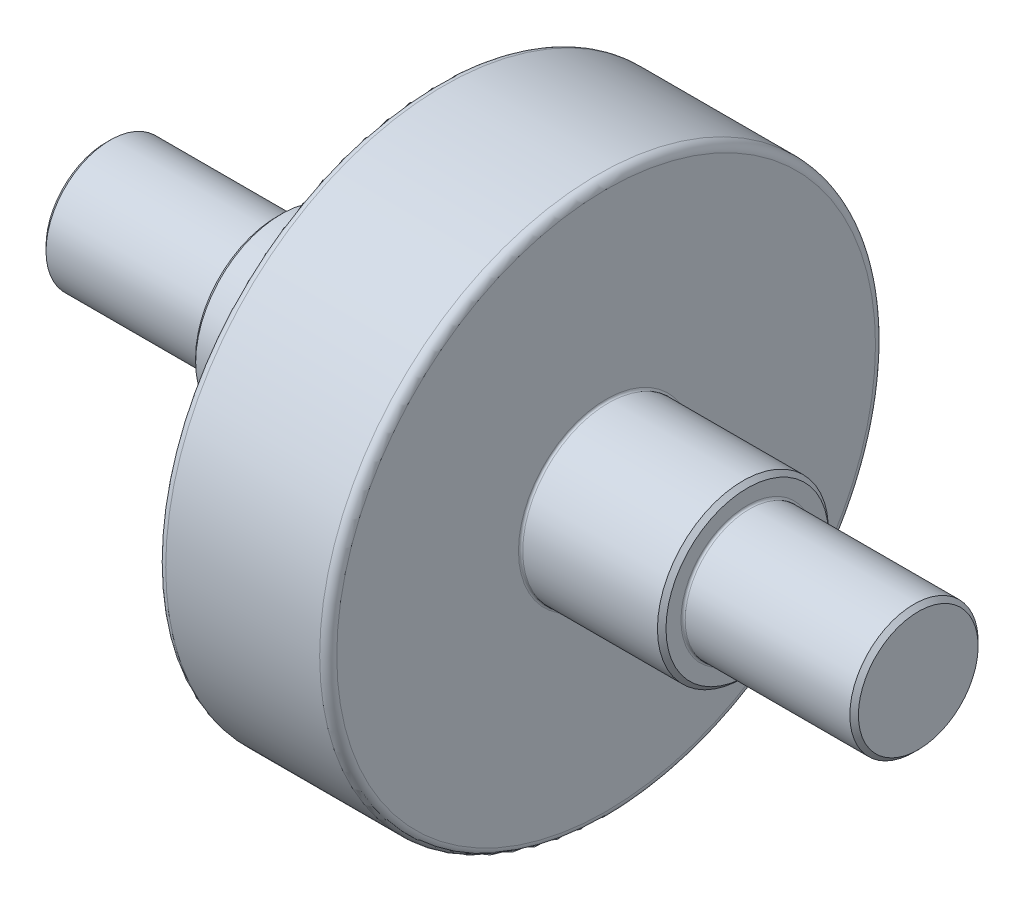
SolidWorks part; units mm, degrees
material "AISI 1045 钢，冷拔"
ref_plane "前视基准面" through (0, 0, 0) normal (0, 0, 1) x (1, 0, 0)
ref_plane "上视基准面" through (0, 0, 0) normal (0, 1, 0) x (1, 0, 0)
ref_plane "右视基准面" through (0, 0, 0) normal (1, 0, 0) x (0, 0, -1)
sketch "草图1" plane through (0, 0, 0) normal (0, 0, 1) x (1, 0, 0)
  line L0 (0, 0) -> (430.5694, 0) construction
  line L2 (0, 0) -> (190, 0)
  line L3 (0, 0) -> (0, 14)
  line L4 (1, 15) -> (39.5, 15)
  line L5 (190, 0) -> (190, 14)
  line L6 (40, 15.5) -> (40, 19)
  line L7 (150, 15.5) -> (150, 19)
  line L8 (41, 20) -> (76.5, 20)
  line L12 (-5, -5) -> (-5, 20) construction
  line L13 (-5, -5) -> (195, -5) construction
  line L14 (195, -5) -> (195, 20) construction
  line L17 (79, 65) -> (115, 65)
  line L19 (-50, -50) -> (-50, 65) construction
  line L20 (-50, -50) -> (240, -50) construction
  line L21 (240, -50) -> (240, 65) construction
  line L22 (77, 20.5) -> (77, 63)
  line L23 (-50, 65) -> (240, 65) construction
  line L24 (-5, 20) -> (195, 20) construction
  line L25 (117, 20.5) -> (117, 63)
  line L31 (150.5, 15) -> (189, 15)
  line L32 (0, 15) -> (190, 15) construction
  line L33 (117.5, 20) -> (149, 20)
  line L35 (0, 0) -> (0, 15) construction
  line L36 (0, 14) -> (1, 15)
  line L37 (40, 19) -> (41, 20)
  line L38 (149, 20) -> (150, 19)
  line L39 (190, 0) -> (190, 15) construction
  line L40 (189, 15) -> (190, 14)
  arc A0 (150, 15.5) -> (150.5, 15) centre (150.5, 15.5) ccw
  arc A1 (117, 20.5) -> (117.5, 20) centre (117.5, 20.5) ccw
  arc A2 (77, 20.5) -> (76.5, 20) centre (76.5, 20.5) cw
  arc A3 (40, 15.5) -> (39.5, 15) centre (39.5, 15.5) cw
  arc A4 (117, 63) -> (115, 65) centre (115, 63) ccw
  arc A5 (77, 63) -> (79, 65) centre (79, 63) cw
  point P0 (190, 7)
  point P7 (50, 15)
  point P8 (50, 204.819)
  point P10 (160, 15)
  point P11 (160, 204.819)
  point P22 (40, 20)
  point P23 (150, 20)
  point P24 (80, 15)
  point P25 (80, 204.819)
  point P26 (130, 15)
  point P27 (130, 204.819)
  point P47 (117, 20)
  dimension "D9" = 0.5
  dimension "D10" = 2
  dimension "D2" = 190
  dimension "D3" = 40
  dimension "D15" = 65
  dimension "D4" = 37
  dimension "D6" = 40
  dimension "D7" = 40
  dimension "D5" = 5
revolve "旋转1" add sketch "草图1" angle 360 about L0
